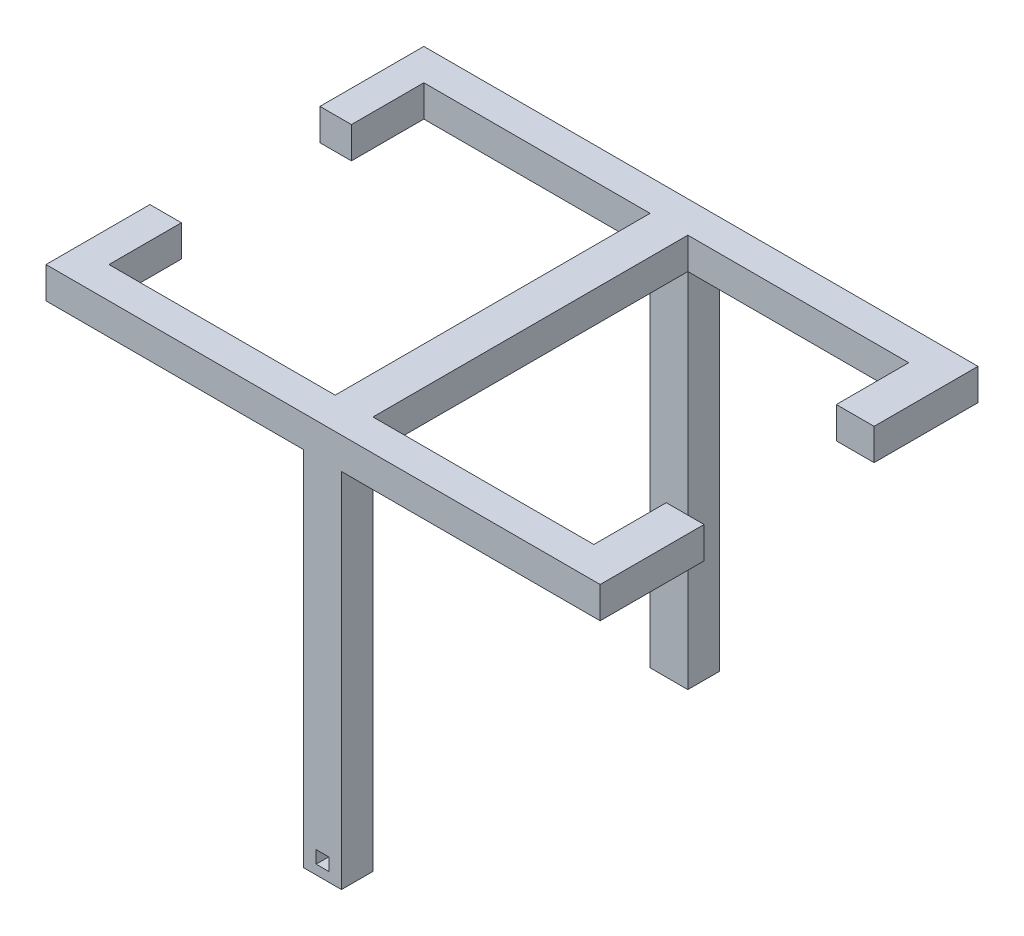
SolidWorks part; units mm, degrees
ref_plane "Front Plane" through (0, 0, 0) normal (0, 0, 1) x (1, 0, 0)
ref_plane "Top Plane" through (0, 0, 0) normal (0, 1, 0) x (1, 0, 0)
ref_plane "Right Plane" through (0, 0, 0) normal (1, 0, 0) x (0, 0, -1)
sketch "Sketch1" plane through (0, 0, 0) normal (0, 0, 1) x (1, 0, 0)
  line L1 (0, 0) -> (176, 0)
  line L2 (0, 0) -> (0, 10)
  line L3 (0, 10) -> (176, 10)
  line L4 (176, 0) -> (176, 10)
  dimension "D1" = 176
  dimension "D2" = 10
extrude "Boss-Extrude1" add sketch "Sketch1" along normal blind 10
sketch "Sketch2" plane through (0, 0, 0) normal (0, 0, -1) x (-1, 0, 0)
  line L1 (0, 0) -> (-176, 0) construction
  line L4 (-81.8453, 10) -> (-93.8453, 10)
  line L5 (-81.8453, 10) -> (-81.8453, 0)
  line L6 (-81.8453, 0) -> (-93.8453, 0)
  line L7 (-93.8453, 10) -> (-93.8453, 0)
  line L8 (-81.8453, 10) -> (-93.8453, 0) construction
  line L9 (-81.8453, 0) -> (-93.8453, 10) construction
  point P6 (-87.8453, 5)
  dimension "D1" = 10
  dimension "D2" = 12
extrude "Boss-Extrude2" add sketch "Sketch2" along normal blind 50
sketch "Sketch3" plane through (0, 0, 0) normal (0, 0, -1) x (-1, 0, 0)
  line L0 (-81.8453, 10) -> (0, 10) construction
  line L1 (0, 0) -> (-10, 0)
  line L2 (0, 0) -> (0, 10)
  line L3 (0, 10) -> (-10, 10)
  line L4 (-10, 0) -> (-10, 10)
  line L5 (-81.8453, 0) -> (-93.8453, 0) construction
  line L6 (-176, 10) -> (-93.8453, 10) construction
  line L7 (-176, 0) -> (-164, 0)
  line L8 (-176, 0) -> (-176, 10)
  line L9 (-176, 10) -> (-164, 10)
  line L10 (-164, 0) -> (-164, 10)
  dimension "D1" = 12
extrude "Boss-Extrude3" add sketch "Sketch3" along normal blind 23
mirror "Mirror6" about plane through (0, 0, -50) normal (0, 0, 1) of bodies 108 109
sketch "Sketch4" plane through (0, 0, 0) normal (0, -1, 0) x (1, 0, 0)
  line L0 (0, 10) -> (176, 10) construction
  line L1 (93.8453, 0) -> (81.8453, 0)
  line L2 (93.8453, 0) -> (93.8453, 10)
  line L3 (93.8453, 10) -> (81.8453, 10)
  line L4 (81.8453, 0) -> (81.8453, 10)
  line L5 (81.8453, -50) -> (93.8453, -50) construction
  line L6 (81.8453, -100) -> (81.8453, 0) construction
  line L7 (93.8453, -100) -> (93.8453, 0) construction
  line L8 (93.8453, -100) -> (93.8453, -110)
  line L9 (93.8453, -110) -> (81.8453, -110)
  line L10 (81.8453, -100) -> (81.8453, -110)
  line L11 (93.8453, -100) -> (81.8453, -100)
extrude "Boss-Extrude4" add sketch "Sketch4" along normal blind 115
sketch "Sketch6" plane through (0, 0, 10) normal (0, 0, 1) x (1, 0, 0)
  line L6 (89.8031, -108.0228) -> (85.8031, -108.0228)
  line L7 (89.8031, -108.0228) -> (89.8031, -112.0228)
  line L8 (89.8031, -112.0228) -> (85.8031, -112.0228)
  line L9 (85.8031, -108.0228) -> (85.8031, -112.0228)
  line L10 (89.8031, -108.0228) -> (85.8031, -112.0228) construction
  line L11 (89.8031, -112.0228) -> (85.8031, -108.0228) construction
  point P7 (87.8031, -110.0228)
  dimension "D3" = 4
  dimension "D4" = 4
extrude "Cut-Extrude1" cut sketch "Sketch6" against normal blind 5
sketch "Sketch7" plane through (0, 0, -110) normal (0, 0, -1) x (-1, 0, 0)
  line L3 (-85.8453, -108) -> (-89.8453, -108)
  line L4 (-85.8453, -108) -> (-85.8453, -112)
  line L5 (-85.8453, -112) -> (-89.8453, -112)
  line L6 (-89.8453, -108) -> (-89.8453, -112)
  line L7 (-85.8453, -108) -> (-89.8453, -112) construction
  line L8 (-85.8453, -112) -> (-89.8453, -108) construction
  dimension "D1" = 4
  dimension "D2" = 4
extrude "Cut-Extrude2" cut sketch "Sketch7" against normal blind 5
